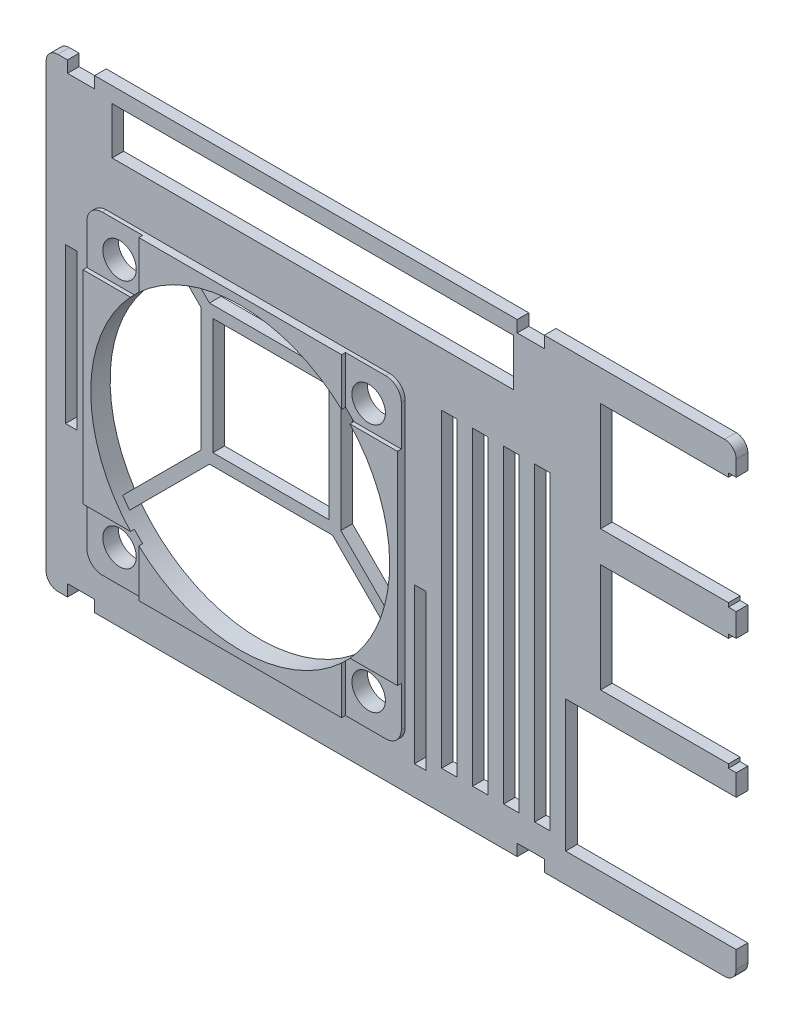
SolidWorks part; units mm, degrees
ref_plane "Front Plane" through (0, 0, 0) normal (0, 0, 1) x (1, 0, 0)
ref_plane "Top Plane" through (0, 0, 0) normal (0, 1, 0) x (1, 0, 0)
ref_plane "Right Plane" through (0, 0, 0) normal (1, 0, 0) x (0, 0, -1)
sketch "Sketch1" plane through (0, 0, 0) normal (0, 0, 1) x (1, 0, 0)
  line L0 (53.5, -5.5) -> (55.5, -5.5) construction
  line L1 (-4, 54.5) -> (82, 54.5)
  line L2 (-5.5, 53) -> (-5.5, -4)
  line L3 (-4, -5.5) -> (82, -5.5)
  line L4 (83.5, 53) -> (83.5, -4)
  line L5 (-5.5, 53) -> (-5.5, -4) construction
  line L6 (83.5, 54.5) -> (-5.5, 54.5) construction
  line L7 (83.5, 51.25) -> (83.5, 53) construction
  arc A0 (-5.5, -4) -> (-4, -5.5) centre (-4, -4) ccw
  arc A1 (-4, 54.5) -> (-5.5, 53) centre (-4, 53) ccw
  arc A2 (82, 54.5) -> (83.5, 53) centre (82, 53) cw
  arc A3 (82, -5.5) -> (83.5, -4) centre (82, -4) ccw
  dimension "D1" = 1.5
extrude "Boss-Extrude1" add sketch "Sketch1" along normal up to surface (1.5 mm away)
sketch "Sketch2" plane through (0, 0, 1.5) normal (0, 0, 1) x (1, 0, 0)
  line L0 (83.5, -4) -> (83.5, 53) construction
  line L1 (83.5, -1.75) -> (61.5, -1.75)
  line L2 (83.5, -1.75) -> (83.5, 15.25)
  line L3 (83.5, 15.25) -> (61.5, 15.25)
  line L4 (61.5, -1.75) -> (61.5, 15.25)
  line L5 (14.5, 19.5607) -> (14.5, 35.4393)
  line L6 (83.5, 18) -> (82.5, 18)
  line L7 (83.5, 18) -> (83.5, 33)
  line L8 (32.5, 35.0819) -> (32.5, 19.5607)
  line L9 (66, 18.5) -> (66, 32.5)
  line L10 (66, 36.5) -> (82.5, 36.5)
  line L11 (82.5, 36.5) -> (82.5, 36)
  line L12 (82.5, 36) -> (83.5, 36)
  line L13 (66, 36.5) -> (66, 50.5)
  line L14 (32.5, 19.5607) -> (38.6535, 13.4071)
  line L15 (16, 20) -> (31, 20)
  line L16 (16, 20) -> (16, 35)
  line L17 (16, 35) -> (31, 35)
  line L18 (3, 46.42) -> (54.8, 46.42)
  line L19 (3, 46.42) -> (3, 52.5)
  line L20 (3, 52.5) -> (54.8, 52.5)
  line L21 (54.8, 46.42) -> (54.8, 52.5)
  line L22 (15.5607, 36.5) -> (30.4509, 36.5)
  line L23 (14.5, 19.5607) -> (4.3805, 9.4412)
  line L24 (33.8248, -0.0558) -> (7.231, -0.0558) construction
  line L25 (54.3, 47.67) -> (54.3, 51.25) construction
  line L26 (3.5, 51.25) -> (3.5, 47.67) construction
  line L27 (4.25, 46.92) -> (5.29, 46.92) construction
  line L28 (5.29, 52) -> (4.25, 52) construction
  line L29 (62, -1.25) -> (83, -1.25) construction
  line L30 (62, 14.75) -> (62, -1.25) construction
  line L31 (83, 14.75) -> (62, 14.75) construction
  line L32 (14.5, 35.4393) -> (12.4592, 37.4802)
  line L33 (5.2613, 8.2006) -> (15.5607, 18.5)
  line L34 (66.5, 32) -> (66.5, 19) construction
  line L35 (66.5, 50) -> (66.5, 37) construction
  line L36 (15.5607, 18.5) -> (31.4393, 18.5)
  line L37 (31.4393, 18.5) -> (38.036, 11.9034)
  line L38 (82.5, 18) -> (82.5, 18.5)
  line L39 (82.5, 18.5) -> (66, 18.5)
  line L40 (82.5, 32.5) -> (82.5, 33)
  line L41 (82.5, 33) -> (83.5, 33)
  line L42 (82.5, 32.5) -> (66, 32.5)
  line L43 (83.5, 32) -> (66.5, 32) construction
  line L44 (66.5, 19) -> (83.5, 19) construction
  line L45 (83.5, 36) -> (83.5, 51)
  line L46 (83.5, 51) -> (82.5, 51)
  line L47 (82.5, 51) -> (82.5, 50.5)
  line L48 (82.5, 50.5) -> (66, 50.5)
  line L49 (66.5, 37) -> (83.5, 37) construction
  line L50 (83.5, 50) -> (66.5, 50) construction
  line L51 (15.5607, 36.5) -> (13.9629, 38.0977)
  line L52 (31, 20) -> (31, 35)
  line L53 (82, -5.5) -> (-4, -5.5) construction
  line L54 (55.25, -4) -> (58.75, -4)
  line L55 (55.25, -4) -> (55.25, -5.5)
  line L56 (55.25, -5.5) -> (58.75, -5.5)
  line L57 (32.5, 19.5607) -> (31.4393, 18.5) construction
  line L58 (14.5, 19.5607) -> (15.5607, 18.5) construction
  line L59 (15.5607, 36.5) -> (14.5, 35.4393) construction
  line L60 (30.5, 33.5) -> (30.5, 34.5) construction
  line L61 (-4, 54.5) -> (82, 54.5) construction
  line L62 (-2.75, 54.5) -> (0.75, 54.5)
  line L63 (-2.75, 54.5) -> (-2.75, 53)
  line L64 (-2.75, 53) -> (0.75, 53)
  line L65 (0.5, -4) -> (-2.5, -4) construction
  line L66 (-2.75, -4) -> (0.75, -4)
  line L67 (-2.75, -4) -> (-2.75, -5.5)
  line L68 (-2.75, -5.5) -> (0.75, -5.5)
  line L69 (58.75, -4) -> (58.75, -5.5)
  line L70 (58.5, -4) -> (55.5, -4) construction
  line L71 (0.75, -4) -> (0.75, -5.5)
  line L72 (0.75, 54.5) -> (0.75, 53)
  line L73 (55.5, 53) -> (58.5, 53) construction
  line L74 (55.25, 54.5) -> (58.75, 54.5)
  line L75 (55.25, 54.5) -> (55.25, 53)
  line L76 (55.25, 53) -> (58.75, 53)
  line L77 (-2.5, 53) -> (0.5, 53) construction
  line L78 (30.5, 34.5) -> (16.5, 34.5) construction
  line L79 (16.5, 34.5) -> (16.5, 33.5) construction
  line L80 (16.5, 20.5) -> (30.5, 20.5) construction
  line L81 (58.75, 54.5) -> (58.75, 53)
  line L82 (58.5, 53) -> (58.5, 54.5) construction
  line L83 (55.5, 54.5) -> (55.5, 53) construction
  line L84 (0.5, 53) -> (0.5, 54.5) construction
  line L85 (-3, 33.75) -> (-1.5, 33.75)
  line L86 (-3, 33.75) -> (-3, 13.75)
  line L87 (-3, 13.75) -> (-1.5, 13.75)
  line L88 (-1.5, 33.75) -> (-1.5, 13.75)
  line L89 (42, 18.25) -> (43.5, 18.25)
  line L90 (42, 18.25) -> (42, -1.75)
  line L91 (42, -1.75) -> (43.5, -1.75)
  line L92 (43.5, 18.25) -> (43.5, -1.75)
  line L93 (-0.5, 32.25) -> (1, 32.25) construction
  line L94 (-5.5, 53) -> (-5.5, -4) construction
  line L95 (-2.5, 54.5) -> (-2.5, 53) construction
  line L96 (41, -0.25) -> (39.5, -0.25) construction
  line L97 (-2.5, -4) -> (-2.5, -5.5) construction
  line L98 (0.5, -5.5) -> (0.5, -4) construction
  line L99 (55.5, -4) -> (55.5, -5.5) construction
  line L100 (58.5, -5.5) -> (58.5, -4) construction
  line L101 (49.5, 39.5) -> (51.5, 39.5)
  line L102 (45.5, 39.5) -> (47.5, 39.5)
  line L103 (45.5, 39.5) -> (45.5, -0.5)
  line L104 (45.5, -0.5) -> (47.5, -0.5)
  line L105 (47.5, 39.5) -> (47.5, -0.5)
  line L106 (49.5, 39.5) -> (49.5, -0.5)
  line L107 (49.5, -0.5) -> (51.5, -0.5)
  line L108 (51.5, 39.5) -> (51.5, -0.5)
  line L109 (53.5, 39.5) -> (55.5, 39.5)
  line L110 (53.5, 39.5) -> (53.5, -0.5)
  line L111 (53.5, -0.5) -> (55.5, -0.5)
  line L112 (55.5, 39.5) -> (55.5, -0.5)
  line L113 (57.5, 39.5) -> (59.5, 39.5)
  line L114 (57.5, 39.5) -> (57.5, -0.5)
  line L115 (57.5, -0.5) -> (59.5, -0.5)
  line L116 (59.5, 39.5) -> (59.5, -0.5)
  arc A0 (4.3805, 9.4412) -> (12.4592, 37.4802) centre (20.5279, 19.9721) cw
  circle A1 centre (20.5279, 19.9721) radius 8 construction
  arc A2 (13.9629, 38.0977) -> (30.4509, 36.5) centre (20.5279, 19.9721) cw
  arc A3 (5.2613, 8.2006) -> (38.036, 11.9034) centre (20.5279, 19.9721) ccw
  arc A4 (38.6535, 13.4071) -> (32.5, 35.0819) centre (20.5279, 19.9721) ccw
  point P84 (16.5, 34)
  point P120 (-2.25, 33.75)
  dimension "D5" = 0.5
  dimension "D6" = 0.5
  dimension "D7" = 0.5
  dimension "D8" = 0.5
  dimension "D9" = 0.5
  dimension "D10" = 0.5
  dimension "D11" = 0.5
  dimension "D14" = 0.5
  dimension "D15" = 0.5
  dimension "D13" = 0.5
  dimension "D18" = 1
  dimension "D19" = 1
  dimension "D12" = 1
  dimension "D20" = 1
  dimension "D21" = 0.5
  dimension "D16" = 0.5
  dimension "D17" = 0.5
  dimension "D22" = 1
  dimension "D23" = 1
  dimension "D24" = 1
  dimension "D25" = 1
  dimension "D29" = 1.5
  dimension "D30" = 1.5
  dimension "D31" = 1.5
  dimension "D32" = 1.5
  dimension "D33" = 1.5
  dimension "D34" = 1.5
  dimension "D35" = 1.5
  dimension "D36" = 135
  dimension "D37" = 135
  dimension "D38" = 135
  dimension "D44" = 20
  dimension "D45" = 1.5
  dimension "D46" = 1.5
  dimension "D47" = 2.5
  dimension "D48" = 40
  dimension "D49" = 1.5
  dimension "D26" = 0.5
  dimension "D27" = 0.5
  dimension "D28" = 0.5
  dimension "D39" = 0.5
  dimension "D40" = 0.75
  dimension "D41" = 0.25
  dimension "D42" = 0.25
  dimension "D43" = 0.25
  dimension "D50" = 0.25
  dimension "D51" = 0.25
  dimension "D52" = 0.25
  dimension "D53" = 0.25
  dimension "D54" = 0.25
  dimension "D55" = 2
  dimension "D56" = 40
  dimension "D57" = 5
  dimension "D58" = 2
  dimension "D59" = 4
extrude "Cut-Extrude1" cut sketch "Sketch2" against normal up to next
sketch "Sketch4" plane through (0, 0, 1.5) normal (0, 0, 1) x (1, 0, 0)
  line L0 (0.5, 6.6752) -> (0.5, 33.269) construction
  line L1 (38.8058, 40.25) -> (2.25, 40.25)
  line L2 (40.8058, 38.25) -> (40.8058, 1.6942)
  line L3 (38.8058, -0.3058) -> (2.25, -0.3058)
  line L4 (0.25, 38.25) -> (0.25, 1.6942)
  line L5 (33.8248, -0.0558) -> (7.231, -0.0558) construction
  line L6 (11.2442, 40) -> (33.8248, 40) construction
  line L7 (40.5558, 33.269) -> (40.5558, 6.6752) construction
  circle A0 centre (20.5279, 19.9721) radius 19.2779
  circle A1 centre (20.5279, 19.9721) radius 8 construction
  arc A2 (38.8058, 40.25) -> (40.8058, 38.25) centre (38.8058, 38.25) cw
  arc A3 (2.25, 40.25) -> (0.25, 38.25) centre (2.25, 38.25) ccw
  arc A4 (40.8058, 1.6942) -> (38.8058, -0.3058) centre (38.8058, 1.6942) cw
  arc A5 (2.25, -0.3058) -> (0.25, 1.6942) centre (2.25, 1.6942) cw
  arc A6 (5.2613, 8.2006) -> (38.036, 11.9034) centre (20.5279, 19.9721) ccw construction
  dimension "D6" = 2
  dimension "D1" = 0.25
  dimension "D2" = 0.25
  dimension "D3" = 0.25
  dimension "D4" = 0.25
extrude "Boss-Extrude2" add sketch "Sketch4" along normal up to surface (1 mm away)
sketch "Sketch5" plane through (0, 0, 2.5) normal (0, 0, 1) x (1, 0, 0)
  circle A0 centre (4.4624, 36.0376) radius 2.159
  circle A1 centre (36.5934, 36.0376) radius 2.159
  circle A2 centre (36.5934, 3.9066) radius 2.159
  circle A3 centre (4.4624, 3.9066) radius 2.159
  circle A4 centre (4.4624, 36.0376) radius 2.159 construction
  circle A5 centre (36.5934, 36.0376) radius 2.159 construction
  circle A6 centre (36.5934, 3.9066) radius 2.159 construction
  circle A7 centre (4.4624, 3.9066) radius 2.159 construction
extrude "Cut-Extrude2" cut sketch "Sketch5" against normal through all
sketch "Sketch6" plane through (0, 0, 2.5) normal (0, 0, 1) x (1, 0, 0)
  line L0 (2.25, -0.3058) -> (38.8058, -0.3058) construction
  line L1 (33.6129, -0.3058) -> (40.8058, -0.3058)
  line L2 (33.6129, -0.3058) -> (33.6129, 6.8871)
  line L3 (33.6129, 6.8871) -> (40.8058, 6.8871)
  line L4 (40.8058, -0.3058) -> (40.8058, 6.8871)
  line L5 (40.8058, 1.6942) -> (40.8058, 38.25) construction
  line L6 (38.8058, 40.25) -> (2.25, 40.25) construction
  line L7 (40.8058, 33.0571) -> (33.6129, 33.0571)
  line L8 (40.8058, 33.0571) -> (40.8058, 40.25)
  line L9 (40.8058, 40.25) -> (33.6129, 40.25)
  line L10 (33.6129, 33.0571) -> (33.6129, 40.25)
  line L11 (0.25, 38.25) -> (0.25, 1.6942) construction
  line L12 (7.4429, -0.3058) -> (0.25, -0.3058)
  line L13 (7.4429, -0.3058) -> (7.4429, 6.8871)
  line L14 (7.4429, 6.8871) -> (0.25, 6.8871)
  line L15 (0.25, -0.3058) -> (0.25, 6.8871)
  line L16 (7.1929, 2.0526) -> (7.1929, -0.0177) construction
  line L17 (0.25, 33.0571) -> (7.4429, 33.0571)
  line L18 (0.25, 33.0571) -> (0.25, 40.25)
  line L19 (0.25, 40.25) -> (7.4429, 40.25)
  line L20 (7.4429, 33.0571) -> (7.4429, 40.25)
  line L21 (0.5381, 6.6371) -> (2.6084, 6.6371) construction
  line L22 (33.8629, -0.0177) -> (33.8629, 2.0526) construction
  line L23 (38.4474, 6.6371) -> (40.5177, 6.6371) construction
  line L24 (40.5177, 33.3071) -> (38.4474, 33.3071) construction
  line L25 (33.8629, 37.8916) -> (33.8629, 39.9619) construction
  line L26 (7.1929, 39.9619) -> (7.1929, 37.8916) construction
  line L27 (2.6084, 33.3071) -> (0.5381, 33.3071) construction
  dimension "D1" = 0.25
  dimension "D2" = 0.25
  dimension "D3" = 0.25
  dimension "D4" = 0.25
  dimension "D5" = 0.25
  dimension "D6" = 0.25
  dimension "D7" = 0.25
  dimension "D8" = 0.25
extrude "Cut-Extrude3" cut sketch "Sketch6" against normal up to surface (0.5 mm away)
equation "\"snap_tol\"=0.25"
equation "\"D50@Sketch2\"=\"snap_tol\""
equation "\"D43@Sketch2\"=\"snap_tol\""
equation "\"D42@Sketch2\"=\"snap_tol\""
equation "\"D41@Sketch2\"=\"snap_tol\""
equation "\"D53@Sketch2\"=\"snap_tol\""
equation "\"D54@Sketch2\"=\"snap_tol\""
equation "\"D51@Sketch2\"=\"snap_tol\""
equation "\"D52@Sketch2\"=\"snap_tol\""
